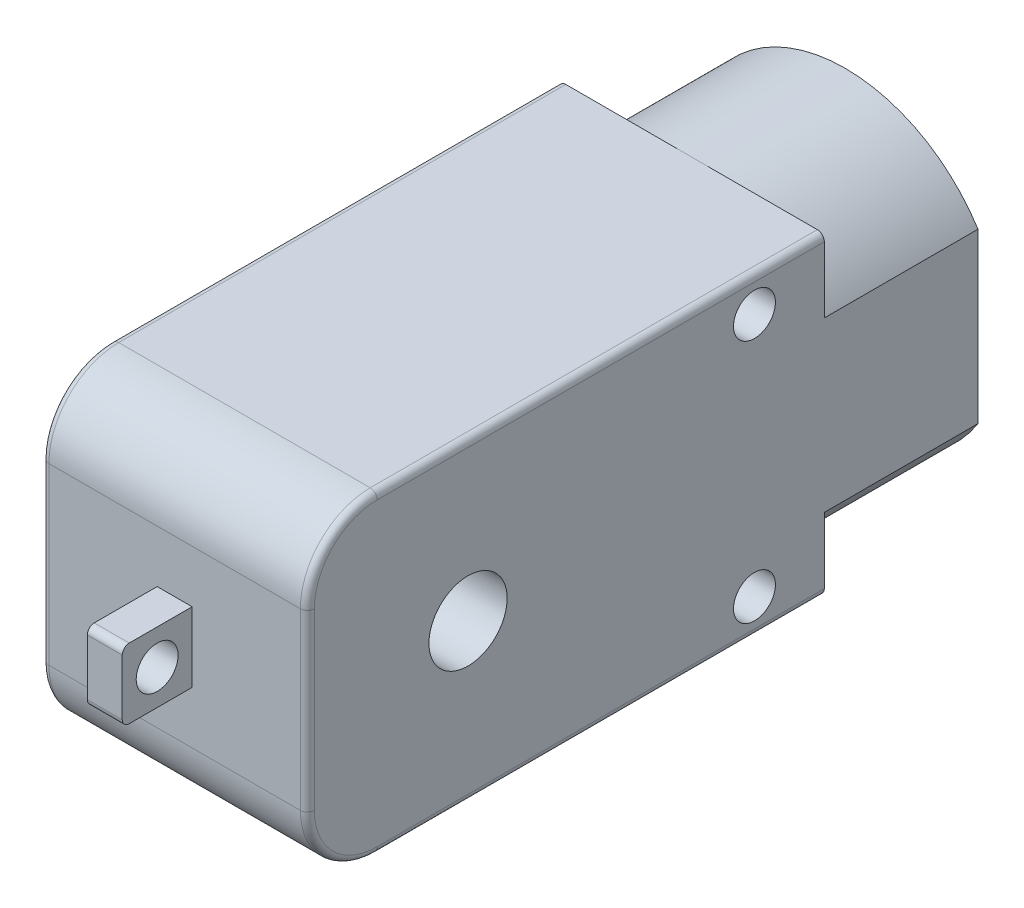
SolidWorks part; units mm, degrees
ref_plane "Front Plane" through (0, 0, 0) normal (0, 0, 1) x (1, 0, 0)
ref_plane "Top Plane" through (0, 0, 0) normal (0, 1, 0) x (1, 0, 0)
ref_plane "Right Plane" through (0, 0, 0) normal (1, 0, 0) x (0, 0, -1)
sketch "Sketch1" plane through (0, 0, 0) normal (0, 0, 1) x (1, 0, 0)
  line L1 (9.5, 11.25) -> (-9.5, 11.25)
  line L2 (9.5, 11.25) -> (9.5, -11.25)
  line L3 (9.5, -11.25) -> (-9.5, -11.25)
  line L4 (-9.5, 11.25) -> (-9.5, -11.25)
  line L5 (9.5, 11.25) -> (-9.5, -11.25) construction
  line L6 (9.5, -11.25) -> (-9.5, 11.25) construction
  point P0 (0, 0)
  dimension "D1" = 22.5
  dimension "D2" = 19
extrude "Boss-Extrude1" add sketch "Sketch1" along normal blind 37
sketch "Sketch2" plane through (0, 0, 0) normal (0, 0, -1) x (-1, 0, 0)
  line L0 (9.5, 6.026) -> (9.5, -6.026)
  line L1 (9.5, 11.25) -> (9.5, -11.25) construction
  line L2 (-9.5, 6.026) -> (-9.5, -6.026)
  arc A0 (9.5, 6.026) -> (-9.5, 6.026) centre (0, 0) ccw
  arc A1 (-9.5, -6.026) -> (9.5, -6.026) centre (0, 0) ccw
extrude "Boss-Extrude2" add sketch "Sketch2" along normal blind 11
fillet "Fillet1" radius 5 2 edges at (0, -11.25, 37) (0, 11.25, 37)
sketch "Sketch3" plane through (9.5, 0, 0) normal (1, 0, 0) x (0, 0, -1)
  circle A0 centre (-5, 8.75) radius 1.5
  circle A1 centre (-5, -8.75) radius 1.5
  dimension "D1" = 17.5
  dimension "D3" = 3
  dimension "D2" = 8.75
  dimension "D4" = 5
  dimension "D5" = 0
extrude "Cut-Extrude1" cut sketch "Sketch3" against normal through all
sketch "Sketch4" plane through (0, 0, 37) normal (0, 0, 1) x (1, 0, 0)
  line L1 (1.25, 2.5) -> (-1.25, 2.5)
  line L2 (1.25, 2.5) -> (1.25, -2.5)
  line L3 (1.25, -2.5) -> (-1.25, -2.5)
  line L4 (-1.25, 2.5) -> (-1.25, -2.5)
  line L5 (1.25, 2.5) -> (-1.25, -2.5) construction
  line L6 (1.25, -2.5) -> (-1.25, 2.5) construction
  point P0 (0, 0)
  dimension "D1" = 2.5
  dimension "D2" = 5
extrude "Boss-Extrude3" add sketch "Sketch4" along normal blind 5
fillet "Fillet2" radius 0.5 12 edges at (0, -2.5, 42) (0, 2.5, 42) (-9.5, -11.25, 16) (-9.5, -9.7855, 35.5355) (-9.5, 0, 37) (-9.5, 9.7855, 35.5355) (9.5, -11.25, 16) (9.5, -9.7855, 35.5355) (9.5, 0, 37) (9.5, 9.7855, 35.5355) (-9.5, 11.25, 16) (9.5, 11.25, 16)
sketch "Sketch5" plane through (1.25, 0, 0) normal (1, 0, 0) x (0, 0, -1)
  line L0 (-41.5, 2.5) -> (-37, 2.5) construction
  line L1 (-42, -2) -> (-42, 2) construction
  circle A0 centre (-39.5, 0) radius 1.5
  dimension "D1" = 3
  dimension "D2" = 2.5
  dimension "D3" = 2.5
extrude "Cut-Extrude2" cut sketch "Sketch5" against normal blind 5
sketch "Sketch6" plane through (9.5, 0, 0) normal (1, 0, 0) x (0, 0, -1)
  circle A0 centre (-25.5, 0) radius 2.8
  dimension "D1" = 5.6
  dimension "D2" = 25.5
extrude "Cut-Extrude3" cut sketch "Sketch6" against normal through all
sketch "Sketch7" plane through (0, 0, -11) normal (0, 0, -1) x (-1, 0, 0)
  line L4 (-8.3, 5.6668) -> (-8.3, -5.6668)
  line L5 (8.3, -5.6668) -> (8.3, 5.6668)
  line L6 (-8.3, 5.6668) -> (-8.3, -5.6668)
  line L7 (8.3, -5.6668) -> (8.3, 5.6668)
  arc A4 (8.3, 5.6668) -> (-8.3, 5.6668) centre (0, 0) ccw
  arc A5 (-8.3, -5.6668) -> (8.3, -5.6668) centre (0, 0) ccw
  arc A6 (8.3, 5.6668) -> (-8.3, 5.6668) centre (0, 0) ccw
  arc A7 (-8.3, -5.6668) -> (8.3, -5.6668) centre (0, 0) ccw
  dimension "D1" = 1.2
extrude "Cut-Extrude4" cut sketch "Sketch7" against normal blind 11
sketch "Sketch8" plane through (0, 0, 0) normal (0, 0, -1) x (-1, 0, 0)
  circle A0 centre (0, 0) radius 3
  dimension "D1" = 6
extrude "Cut-Extrude5" cut sketch "Sketch8" against normal blind 2
